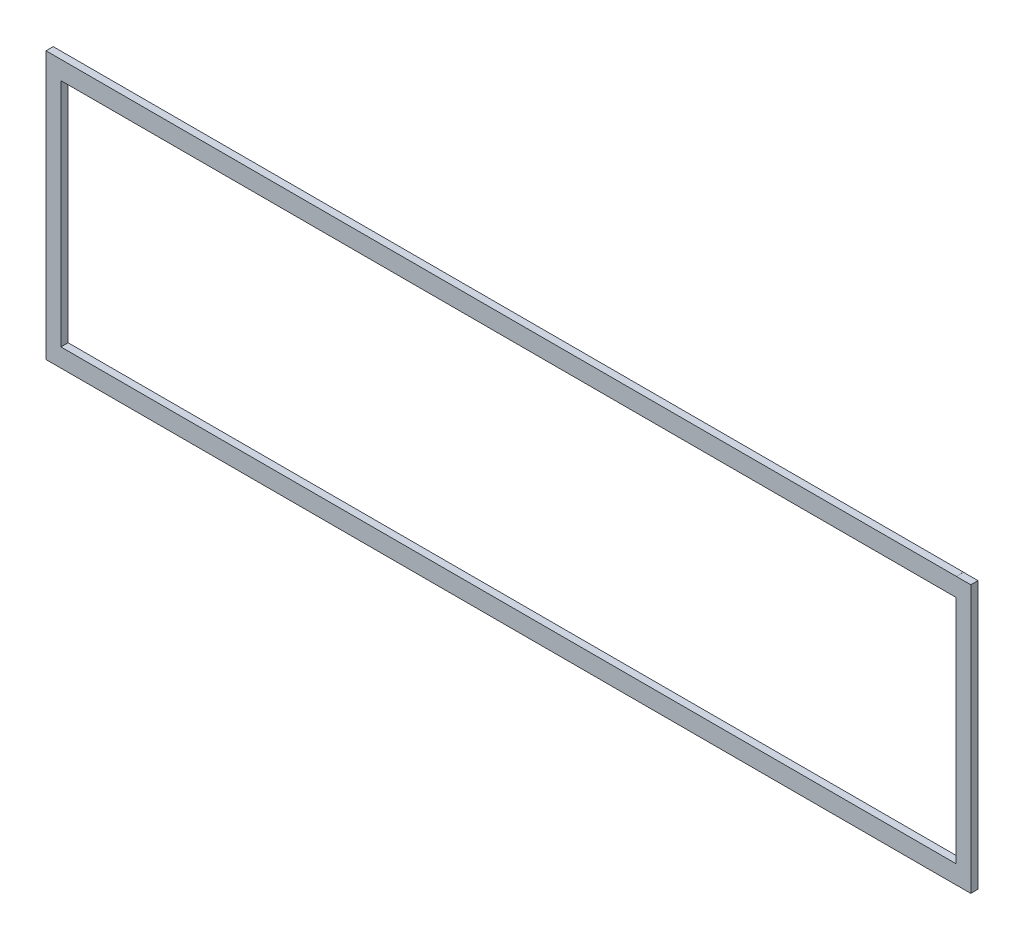
SolidWorks part; units mm, degrees
ref_plane "Front Plane" through (0, 0, 0) normal (0, 0, 1) x (1, 0, 0)
ref_plane "Top Plane" through (0, 0, 0) normal (0, 1, 0) x (1, 0, 0)
ref_plane "Right Plane" through (0, 0, 0) normal (1, 0, 0) x (0, 0, -1)
sketch "Sketch1" plane through (0, 0, 0) normal (0, 0, 1) x (1, 0, 0)
  line L0 (0, 58.6835) -> (406.4, 58.6835) construction
  line L1 (0, 0) -> (400.05, 0)
  line L2 (0, 0) -> (0, 117.3671)
  line L3 (0, 117.3671) -> (400.05, 117.3671)
  line L4 (406.4, 0) -> (406.4, 117.3671)
  line L6 (400.05, 117.3671) -> (400.05, 117.3417)
  line L7 (400.05, 117.3417) -> (406.4, 117.3417)
  line L8 (406.4, 117.3671) -> (406.4, 117.3417)
  line L9 (406.4, 0) -> (406.4, 0.0254)
  line L10 (400.05, 0.0254) -> (406.4, 0.0254)
  line L11 (400.05, 0) -> (400.05, 0.0254)
  line L13 (6.35, 109.4835) -> (400.05, 109.4835)
  line L14 (6.35, 109.4835) -> (6.35, 7.8835)
  line L15 (6.35, 7.8835) -> (400.05, 7.8835)
  line L16 (400.05, 109.4835) -> (400.05, 7.8835)
  point P17 (6.35, 58.6835)
  dimension "D1" = 406.4
  dimension "D2" = 117.3671
  dimension "D3" = 117.3163
  dimension "D4" = 6.35
  dimension "D5" = 6.35
  dimension "D6" = 6.35
  dimension "D7" = 101.6
extrude "Boss-Extrude1" add sketch "Sketch1" along normal blind 3.175 contours L0 L2 L1 L11 L10 L4 L16 L15 L14 | L2 L0 L14 L13 L16 L4 L7 L6 L3
ref_plane "Plane1" through (0, 0, 3.175) normal (0, 0, 1) x (1, 0, 0)
sketch "Sketch2" plane through (0, 0, 3.175) normal (0, 0, 1) x (1, 0, 0)
  line L17 (400.1516, 117.4686) -> (-0.1016, 117.4686)
  line L18 (-0.1016, 117.4686) -> (-0.1016, -0.1016)
  line L19 (-0.1016, -0.1016) -> (400.1516, -0.1016)
  line L20 (400.1516, -0.1016) -> (400.1516, -0.0762)
  line L21 (400.1516, -0.0762) -> (406.5016, -0.0762)
  line L22 (406.5016, -0.0762) -> (406.5016, 117.4433)
  line L23 (406.5016, 117.4433) -> (400.1516, 117.4433)
  line L24 (400.1516, 117.4433) -> (400.1516, 117.4686)
  line L25 (400.1516, 117.4686) -> (-0.1016, 117.4686)
  line L26 (-0.1016, 117.4686) -> (-0.1016, -0.1016)
  line L27 (-0.1016, -0.1016) -> (400.1516, -0.1016)
  line L28 (400.1516, -0.1016) -> (400.1516, -0.0762)
  line L29 (400.1516, -0.0762) -> (406.5016, -0.0762)
  line L30 (406.5016, -0.0762) -> (406.5016, 117.4433)
  line L31 (406.5016, 117.4433) -> (400.1516, 117.4433)
  line L32 (400.1516, 117.4433) -> (400.1516, 117.4686)
  line L39 (399.9484, 7.9851) -> (399.9484, 109.3819)
  line L40 (6.4516, 7.9851) -> (399.9484, 7.9851)
  line L41 (6.4516, 109.3819) -> (6.4516, 7.9851)
  line L42 (399.9484, 109.3819) -> (6.4516, 109.3819)
  line L43 (399.9484, 7.9851) -> (399.9484, 109.3819)
  line L44 (6.4516, 7.9851) -> (399.9484, 7.9851)
  line L45 (6.4516, 109.3819) -> (6.4516, 7.9851)
  line L46 (399.9484, 109.3819) -> (6.4516, 109.3819)
  dimension "D1" = 0.1016
  dimension "D2" = 0.1016
extrude "Boss-Extrude2" add sketch "Sketch2" against normal blind 3.175
equation "\"ROADWIDTH\"=4.62075"
equation "\"TABWIDTH\"=4.61875"
equation "\"D2@Sketch1\"=\"ROADWIDTH\""
equation "\"D3@Sketch1\"=\"TABWIDTH\""
